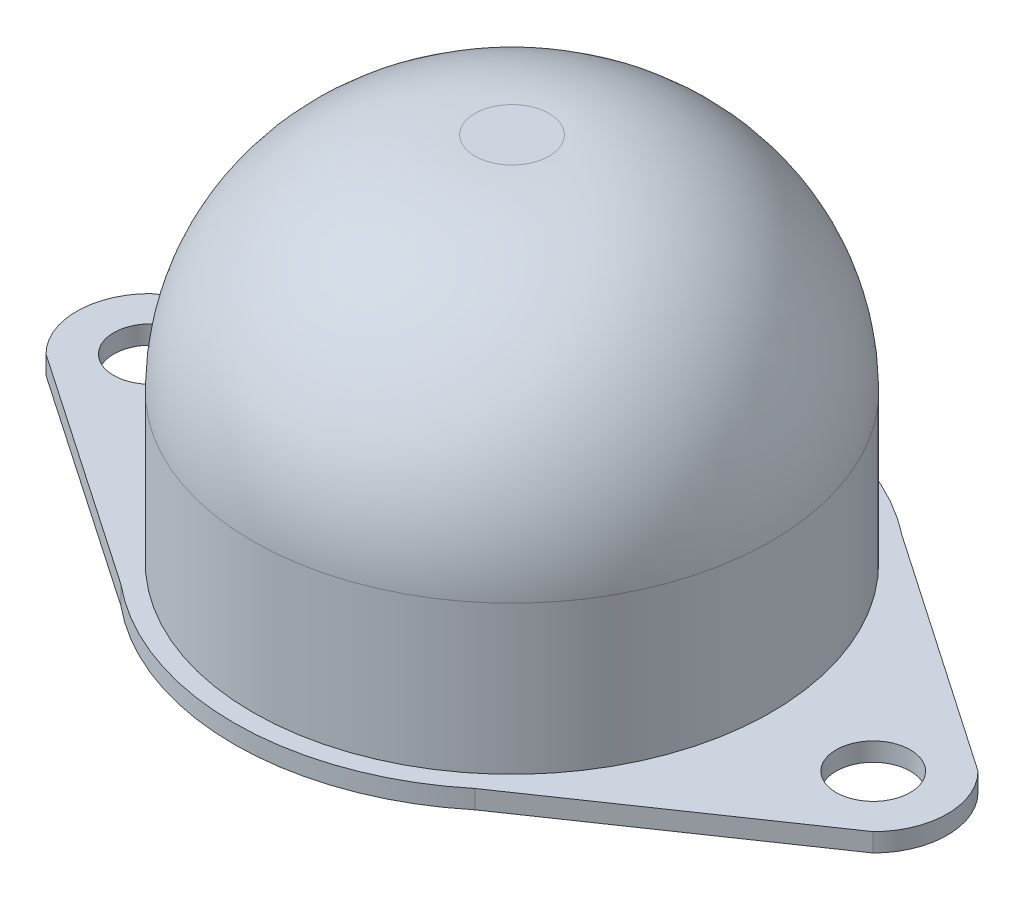
SolidWorks part; units mm, degrees
ref_plane "Front Plane" through (0, 0, 0) normal (0, 0, 1) x (1, 0, 0)
ref_plane "Top Plane" through (0, 0, 0) normal (0, 1, 0) x (1, 0, 0)
ref_plane "Right Plane" through (0, 0, 0) normal (1, 0, 0) x (0, 0, -1)
sketch "Sketch1" plane through (0, 0, 0) normal (0, 1, 0) x (1, 0, 0)
  circle A0 centre (0, 0) radius 14
extrude "Boss-Extrude1" add sketch "Sketch1" along normal blind 20
fillet "Fillet 1" radius 12 1 edges at (0, 20, 14)
sketch "Sketch2" plane through (0, 0, 0) normal (0, -1, 0) x (-1, 0, 0)
  circle A0 centre (0, 0) radius 15
extrude "Boss-Extrude2" add sketch "Sketch2" along normal blind 1
sketch "Sketch3" plane through (0, 0, 0) normal (0, 1, 0) x (1, 0, 0)
  line L0 (-22.3284, 2.8284) -> (-7.6358, 12.911)
  line L1 (-22.3284, -2.8284) -> (-7.3064, -13.1002)
  line L2 (0, -11.55) -> (0, 11.55) construction
  line L3 (22.3284, -2.8284) -> (7.3064, -13.1002)
  line L4 (22.3284, 2.8284) -> (7.6358, 12.911)
  circle A0 centre (-19.5, 0) radius 2
  arc A1 (-23.5, 0) -> (-22.3284, -2.8284) centre (-19.5, 0) ccw
  arc A2 (-23.5, 0) -> (-22.3284, 2.8284) centre (-19.5, 0) cw
  circle A3 centre (0, 0) radius 15 construction
  arc A4 (23.5, 0) -> (22.3284, 2.8284) centre (19.5, 0) ccw
  arc A5 (23.5, 0) -> (22.3284, -2.8284) centre (19.5, 0) cw
  circle A6 centre (19.5, 0) radius 2
  circle M2 centre (0, 0) radius 15
  dimension "D1" = 19.5
extrude "Boss-Extrude3" add sketch "Sketch3" against normal blind 1 contours A2 A1 L1 L0 A0 M2 | A5 A4 L4 L3 A6 M2
